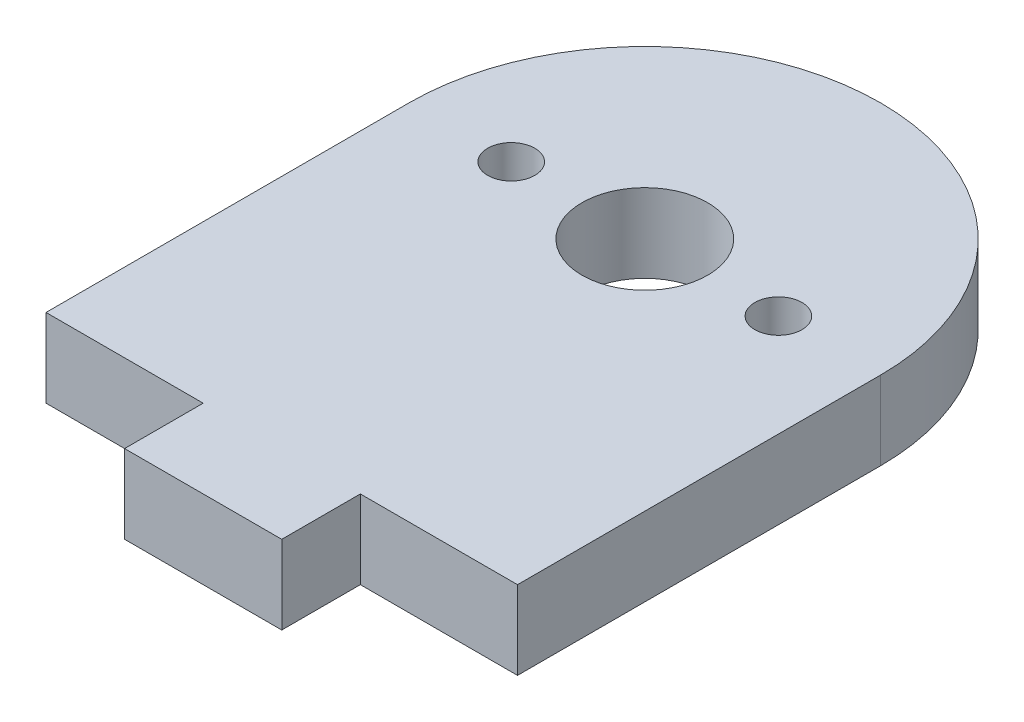
SolidWorks part; units mm, degrees
ref_plane "前视基准面" through (0, 0, 0) normal (0, 0, 1) x (1, 0, 0)
ref_plane "上视基准面" through (0, 0, 0) normal (0, 1, 0) x (1, 0, 0)
ref_plane "右视基准面" through (0, 0, 0) normal (1, 0, 0) x (0, 0, -1)
sketch "草图1" plane through (0, 0, 0) normal (0, 1, 0) x (1, 0, 0)
  line L1 (-15, -11.55) -> (15, -11.55)
  line L2 (-15, -11.55) -> (-15, 11.55)
  line L3 (-15, 11.55) -> (15, 11.55)
  line L4 (15, -11.55) -> (15, 11.55)
  line L5 (-15, -11.55) -> (15, 11.55) construction
  line L6 (-15, 11.55) -> (15, -11.55) construction
  line L7 (15, 11.55) -> (-15, 11.55)
  line L8 (15, 11.55) -> (15, 27.55)
  line L9 (15, 27.55) -> (-15, 27.55)
  line L10 (-15, 11.55) -> (-15, 27.55)
  circle A0 centre (0, 11.55) radius 12.5
  circle A1 centre (0, 11.55) radius 15
  point P0 (0, 0)
  dimension "D3" = 25
  dimension "D1" = 30
  dimension "D2" = 23.1
  dimension "D4" = 16
extrude "凸台-拉伸1" add sketch "草图1" along normal blind 5 contours L3 A1 A0 | L3 A1 A0 | A1 L2 L1 L4
sketch "草图2" plane through (0, 5, 0) normal (0, 1, 0) x (1, 0, 0)
  circle A0 centre (0, 11.55) radius 12.5
  circle A1 centre (0, 11.55) radius 8.5 construction
  circle A2 centre (-8.5, 11.55) radius 1.5
  circle A3 centre (8.5, 11.55) radius 1.5
  circle A4 centre (0, 11.55) radius 4
  dimension "D1" = 17
  dimension "D2" = 3
  dimension "D3" = 3
  dimension "D4" = 8
extrude "凸台-拉伸2" add sketch "草图2" against normal blind 5
sketch "草图3" plane through (0, 5, 0) normal (0, 1, 0) x (1, 0, 0)
  line L0 (-15, -11.55) -> (15, -11.55) construction
  line L1 (-5, -11.55) -> (5, -11.55)
  line L2 (-5, -11.55) -> (-5, -16.55)
  line L3 (-5, -16.55) -> (5, -16.55)
  line L4 (5, -11.55) -> (5, -16.55)
  line L5 (-15, -11.55) -> (-15, 11.55) construction
  line L6 (15, -11.55) -> (15, 11.55) construction
  dimension "D1" = 10
  dimension "D2" = 10
  dimension "D3" = 5
extrude "凸台-拉伸3" add sketch "草图3" against normal blind 5
